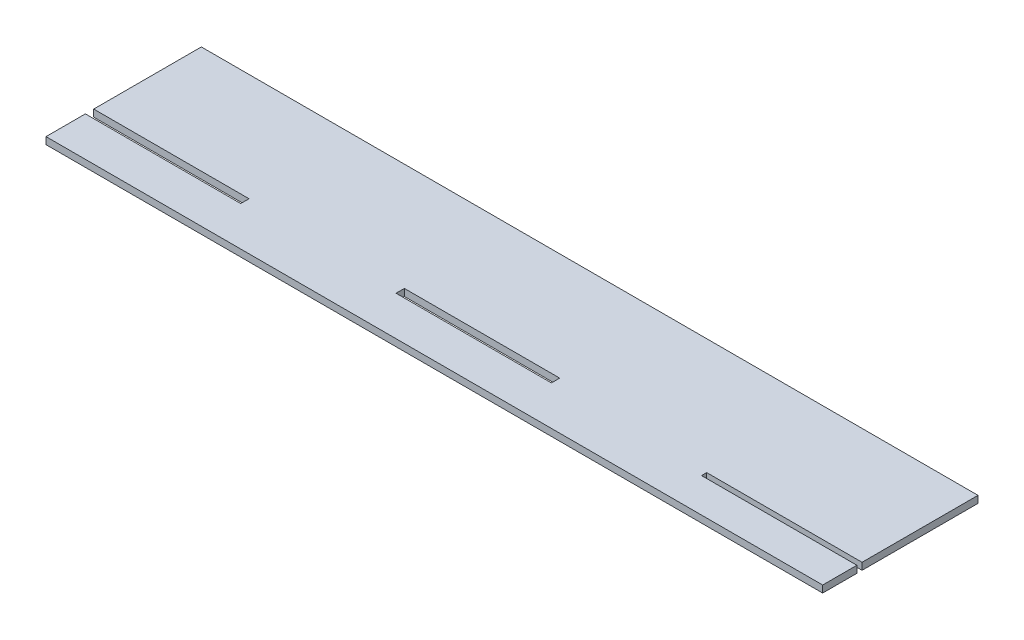
SolidWorks part; units mm, degrees
ref_plane "Front Plane" through (0, 0, 0) normal (0, 0, 1) x (1, 0, 0)
ref_plane "Top Plane" through (0, 0, 0) normal (0, 1, 0) x (1, 0, 0)
ref_plane "Right Plane" through (0, 0, 0) normal (1, 0, 0) x (0, 0, -1)
sketch "Sketch1" plane through (0, 0, 0) normal (0, 1, 0) x (1, 0, 0)
  line L0 (-150, -14.79) -> (-90, -14.79)
  line L1 (-150, 30) -> (150, 30)
  line L2 (-150, 30) -> (-150, -11.572)
  line L3 (-150, -30) -> (150, -30)
  line L4 (150, 30) -> (150, -14.79)
  line L5 (-150, -11.572) -> (-90, -11.572)
  line L6 (90, -14.79) -> (150, -14.79)
  line L7 (-30, -11.572) -> (30, -11.572)
  line L9 (90, -16.782) -> (150, -16.782)
  line L10 (-90, -11.572) -> (-90, -14.79)
  line L11 (-30, -11.572) -> (-30, -14.79)
  line L12 (30, -11.572) -> (30, -14.79)
  line L13 (90, -16.782) -> (90, -14.79)
  line L14 (-150, -14.79) -> (-150, -30)
  line L15 (-30, -14.79) -> (30, -14.79)
  line L16 (150, -16.782) -> (150, -30)
  point P0 (0, 0)
  dimension "D1" = 300
  dimension "D2" = 60
  dimension "D3" = 15.21
  dimension "D4" = 3.218
extrude "Boss-Extrude1" add sketch "Sketch1" along normal blind 2.7
